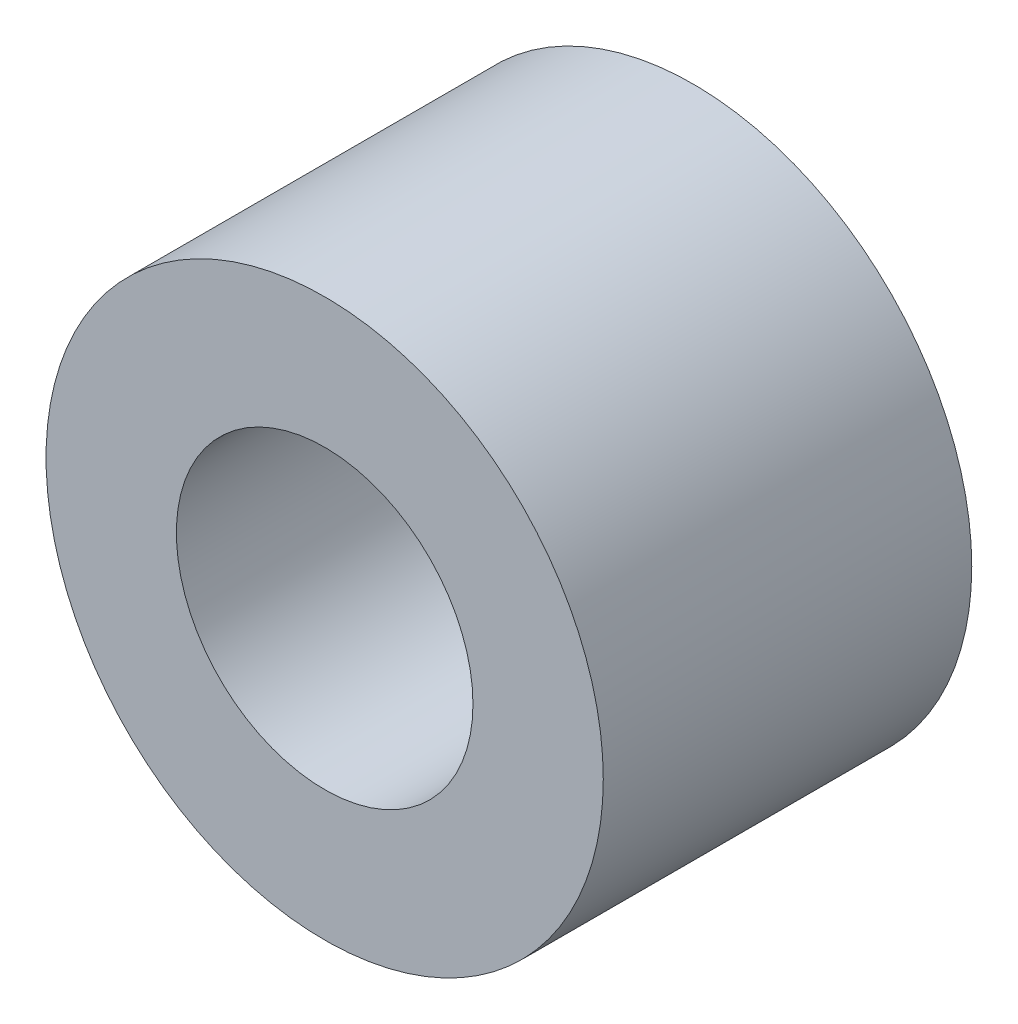
SolidWorks part; units mm, degrees
ref_plane "Front Plane" through (0, 0, 0) normal (0, 0, 1) x (1, 0, 0)
ref_plane "Top Plane" through (0, 0, 0) normal (0, 1, 0) x (1, 0, 0)
ref_plane "Right Plane" through (0, 0, 0) normal (1, 0, 0) x (0, 0, -1)
sketch "Sketch1" plane through (0, 0, 0) normal (0, 0, 1) x (1, 0, 0)
  circle A0 centre (0, 0) radius 1.65
  circle A1 centre (0, 0) radius 3.1
  dimension "D1" = 3.3
  dimension "D2" = 6.2
extrude "Boss-Extrude1" add sketch "Sketch1" along normal blind 4.1
